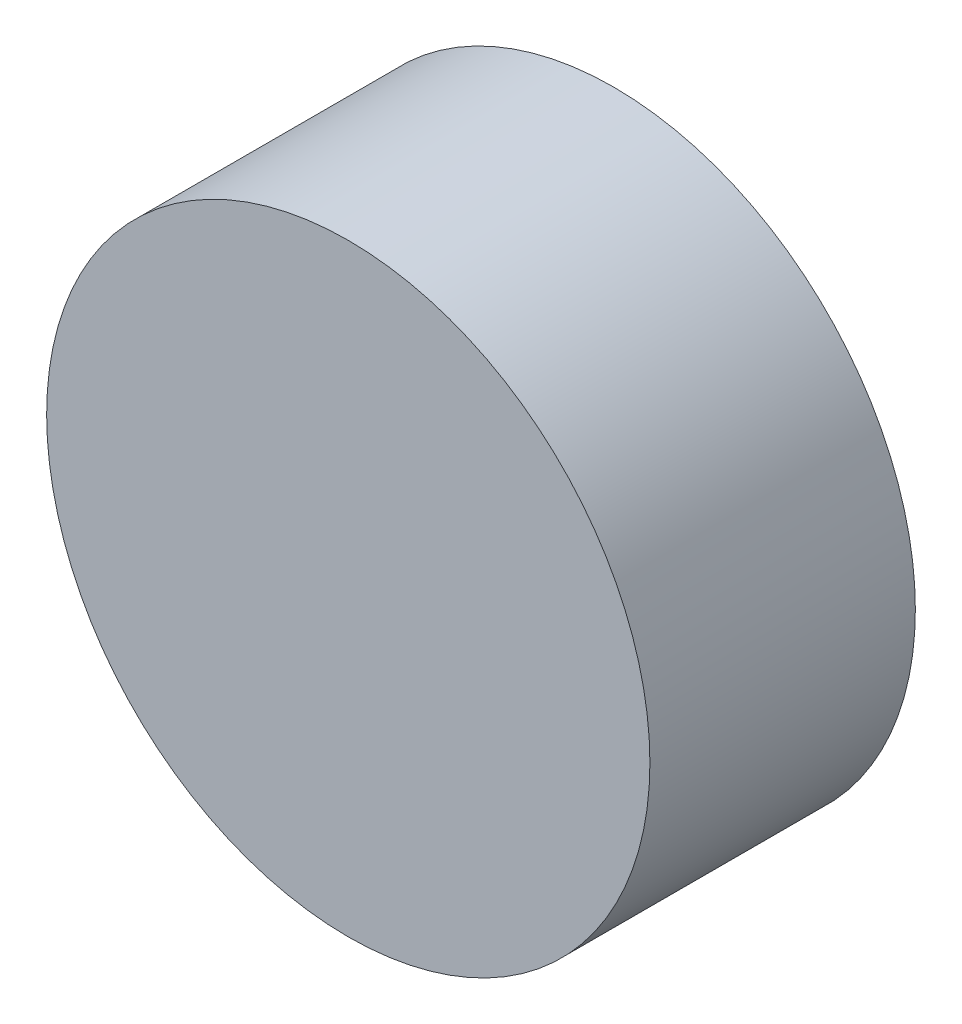
SolidWorks part; units mm, degrees
ref_plane "Front Plane" through (0, 0, 0) normal (0, 0, 1) x (1, 0, 0)
ref_plane "Top Plane" through (0, 0, 0) normal (0, 1, 0) x (1, 0, 0)
ref_plane "Right Plane" through (0, 0, 0) normal (1, 0, 0) x (0, 0, -1)
sketch "Sketch1" plane through (0, 0, 0) normal (0, 0, 1) x (1, 0, 0)
  circle A0 centre (0, 0) radius 12.5
extrude "Boss-Extrude1" add sketch "Sketch1" along normal blind 11
